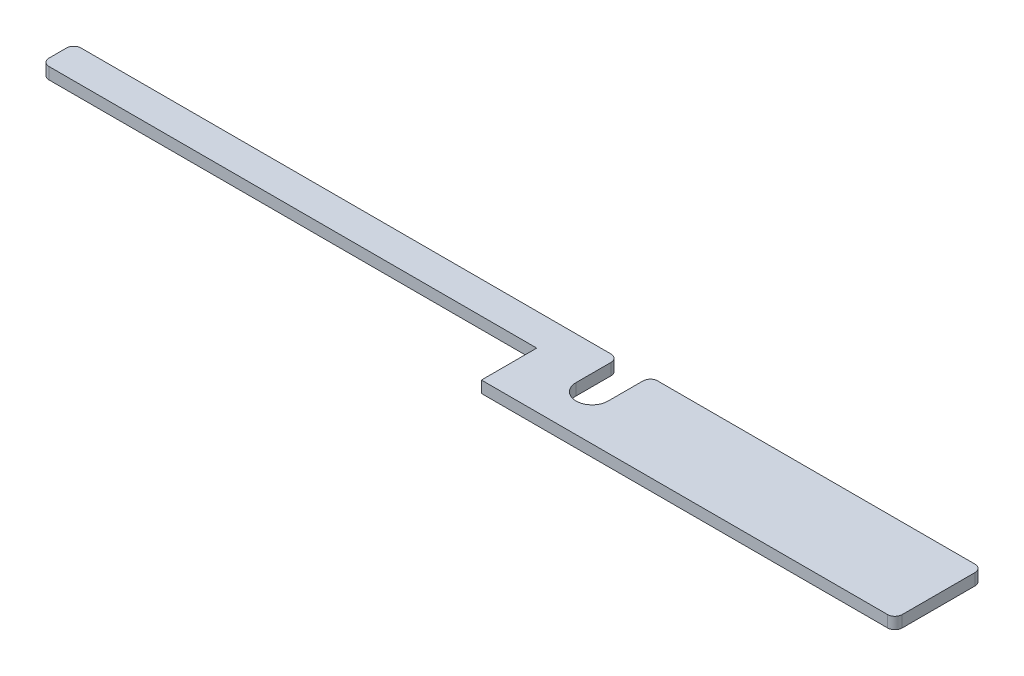
SolidWorks part; units mm, degrees
material "Stainless Steel (ferritic)"
ref_plane "Front Plane" through (0, 0, 0) normal (0, 0, 1) x (1, 0, 0)
ref_plane "Top Plane" through (0, 0, 0) normal (0, 1, 0) x (1, 0, 0)
ref_plane "Right Plane" through (0, 0, 0) normal (1, 0, 0) x (0, 0, -1)
sketch "Sketch1" plane through (0, 0, 0) normal (0, 1, 0) x (1, 0, 0)
  line L0 (0, 0) -> (-36.068, 0)
  line L1 (-36.068, 0) -> (-36.068, 4.826)
  line L2 (-36.068, 4.826) -> (-79.248, 4.826)
  line L3 (-79.248, 4.826) -> (-79.248, 7.62)
  line L4 (-79.248, 7.62) -> (-31.75, 7.62)
  line L5 (-31.75, 7.62) -> (-31.75, 3.937)
  line L6 (-28.956, 3.937) -> (-28.956, 7.62)
  line L7 (-28.956, 7.62) -> (0, 7.62)
  line L8 (0, 7.62) -> (0, 0)
  arc A0 (-31.75, 3.937) -> (-28.956, 3.937) centre (-30.353, 3.937) ccw
  point P10 (-30.353, 2.54)
  dimension "D3" = 1.397
  dimension "D1" = 79.248
  dimension "D2" = 43.18
  dimension "D4" = 5.08
  dimension "D5" = 47.498
  dimension "D6" = 7.62
  dimension "D7" = 2.794
extrude "Boss-Extrude1" add sketch "Sketch1" along normal blind 1.016
fillet "Fillet1" radius 0.635 6 edges at (-79.248, 0.508, -7.62) (-79.248, 0.508, -4.826) (-28.956, 0.508, -7.62) (-31.75, 0.508, -7.62) (0, 0.508, -7.62) (0, 0.508, 0)
